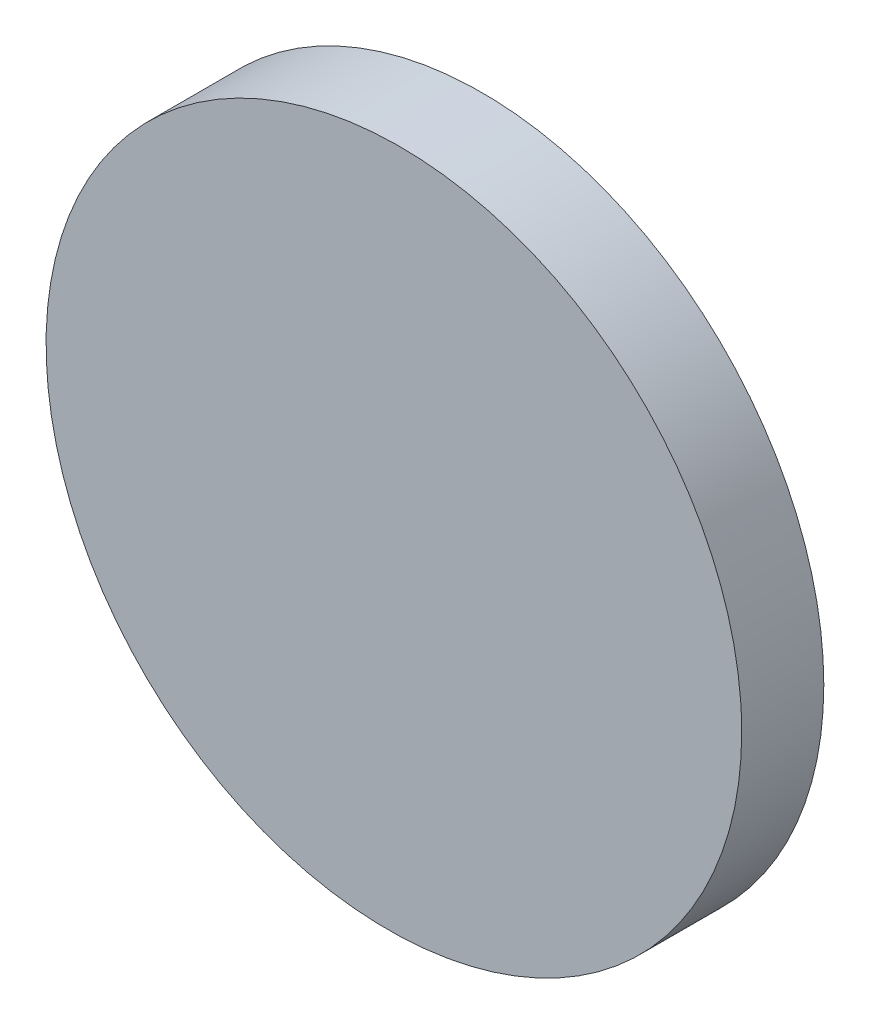
SolidWorks part; units mm, degrees
ref_plane "前视基准面" through (0, 0, 0) normal (0, 0, 1) x (1, 0, 0)
ref_plane "上视基准面" through (0, 0, 0) normal (0, 1, 0) x (1, 0, 0)
ref_plane "右视基准面" through (0, 0, 0) normal (1, 0, 0) x (0, 0, -1)
sketch "草图1" plane through (0, 0, 0) normal (0, 0, 1) x (1, 0, 0)
  circle A0 centre (0, 0) radius 12.5
extrude "凸台-拉伸1" add sketch "草图1" along normal blind 10
sketch "草图2" plane through (0, 0, 0) normal (0, 1, 0) x (1, 0, 0)
  line L0 (12.5, -3) -> (-16.638, -3.4933)
  line L1 (12.5, -10) -> (12.5, 0) construction
  line L2 (-16.638, -3.4933) -> (-16.638, -14.4312)
  line L3 (-16.638, -14.4312) -> (17.7709, -14.4312)
  line L4 (17.7709, -14.4312) -> (17.7709, -3)
  line L5 (17.7709, -3) -> (12.5, -3)
  line L6 (12.5, 0) -> (-12.5, 0) construction
  dimension "D1" = 0.97
  dimension "D2" = 3
extrude "切除-拉伸1" cut sketch "草图2" against normal mid plane 50
